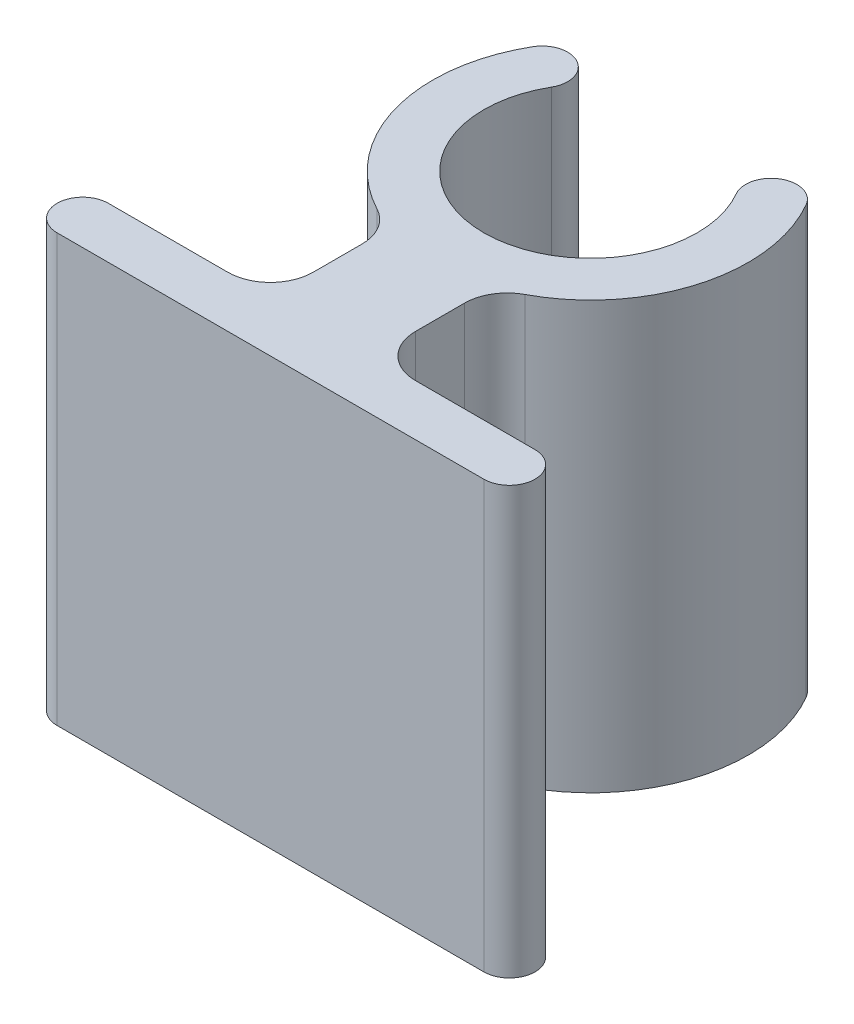
SolidWorks part; units mm, degrees
ref_plane "Front Plane" through (0, 0, 0) normal (0, 0, 1) x (1, 0, 0)
ref_plane "Top Plane" through (0, 0, 0) normal (0, 1, 0) x (1, 0, 0)
ref_plane "Right Plane" through (0, 0, 0) normal (1, 0, 0) x (0, 0, -1)
sketch "Sketch1" plane through (0, 0, 0) normal (0, 1, 0) x (1, 0, 0)
  line L0 (0, -2.5) -> (0, -7.5)
  line L1 (0, -7.5) -> (-5, -7.5)
  line L2 (0, 0) -> (-2.1651, 1.25) construction
  line L3 (0, -2.5) -> (0, 0) construction
  line L4 (-1.2, -3.5) -> (-1.2, -6.3)
  line L5 (-1.2, -6.3) -> (-5, -6.3)
  arc A0 (-2.1651, 1.25) -> (0, -2.5) centre (0, 0) ccw
  arc A1 (-3.2043, 1.85) -> (-1.2, -3.5) centre (0, 0) ccw
  arc A2 (-2.1651, 1.25) -> (-3.2043, 1.85) centre (-2.6847, 1.55) ccw
  arc A3 (-5, -7.5) -> (-5, -6.3) centre (-5, -6.9) cw
  dimension "D1" = 5
  dimension "D2" = 7.5
  dimension "D3" = 5
  dimension "D4" = 120
  dimension "D5" = 1.2
extrude "Boss-Extrude1" add sketch "Sketch1" along normal blind 10
fillet "Fillet1" radius 1 2 edges at (-1.2, 5, 6.3) (-1.2, 5, 3.5)
mirror "Mirror1" about plane through (0, 10, 2.5) normal (-1, 0, 0) of bodies 101
